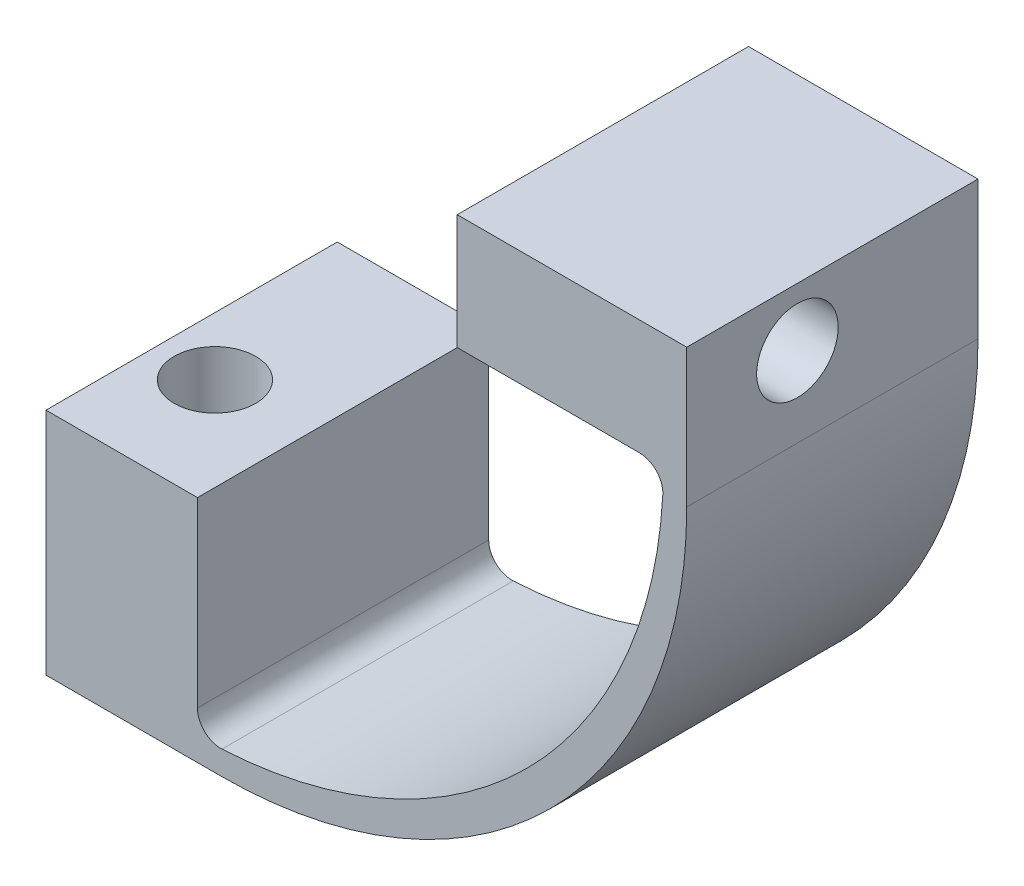
SolidWorks part; units mm, degrees
ref_plane "Front Plane" through (0, 0, 0) normal (0, 0, 1) x (1, 0, 0)
ref_plane "Top Plane" through (0, 0, 0) normal (0, 1, 0) x (1, 0, 0)
ref_plane "Right Plane" through (0, 0, 0) normal (1, 0, 0) x (0, 0, -1)
ref_plane "Plane1" through (50, 0, 0) normal (1, 0, 0) x (0, 0, -1)
sketch "Sketch2" plane through (50, 0, 0) normal (1, 0, 0) x (0, 0, -1)
  line L0 (0, 60.2317) -> (0, -60.2317) construction
  line L1 (47.5464, 0) -> (-47.5464, 0) construction
  line L3 (-9.5, 0) -> (15.5, 0)
  line L4 (-9.5, 0) -> (-9.5, 51.88)
  line L5 (-9.5, 51.88) -> (15.5, 51.88)
  line L6 (15.5, 0) -> (15.5, 51.88)
  circle A0 centre (0, 46.88) radius 3.5
  dimension "D1" = 46.88
  dimension "D2" = 25
  dimension "D3" = 9.5
  dimension "D4" = 5
sketch "Sketch1" plane through (0, 0, 0) normal (0, 1, 0) x (1, 0, 0)
  line L0 (50, -55.6605) -> (50, 55.6605) construction
  line L1 (50, 15.5) -> (-5, 15.5)
  line L2 (50, 15.5) -> (50, -9.5)
  line L3 (50, -9.5) -> (-5, -9.5)
  line L4 (-5, 15.5) -> (-5, -9.5)
  circle A0 centre (0, 0) radius 3.5
  dimension "D1" = 9.5
  dimension "D2" = 25
  dimension "D3" = 5
extrude "Boss-Extrude1" add sketch "Sketch1" along normal blind 2
extrude "Boss-Extrude2" add sketch "Sketch2" against normal blind 2
fillet "Fillet2" radius 40 2 edges at (50, 0, -3) (48, 2, -3)
sketch "Sketch5" plane through (0, 2, 0) normal (0, 1, 0) x (1, 0, 0)
  line L1 (-5, 15.5) -> (8, 15.5)
  line L2 (-5, 15.5) -> (-5, -9.5)
  line L3 (-5, -9.5) -> (8, -9.5)
  line L4 (8, 15.5) -> (8, -9.5)
  circle A0 centre (0, 0) radius 3.5
extrude "Boss-Extrude5" add sketch "Sketch5" along normal blind 17.7
sketch "Sketch6" plane through (48, 0, 0) normal (-1, 0, 0) x (0, 0, 1)
  line L1 (-15.5, 51.88) -> (9.5, 51.88)
  line L2 (-15.5, 51.88) -> (-15.5, 42)
  line L3 (-15.5, 42) -> (9.5, 42)
  line L4 (9.5, 51.88) -> (9.5, 42)
  circle A0 centre (0, 46.88) radius 3.5
extrude "Boss-Extrude6" add sketch "Sketch6" along normal blind 17.7
fillet "Fillet3" radius 2 1 edges at (48, 42, -3)
fillet "Fillet4" radius 2 1 edges at (8, 2, -3)
